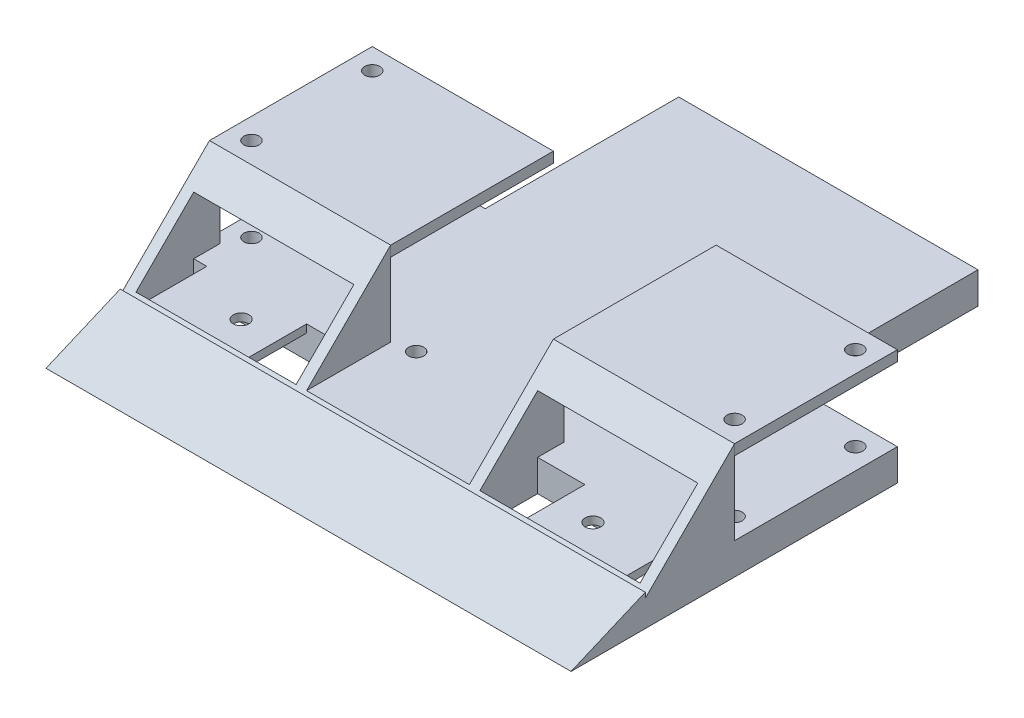
SolidWorks part; units mm, degrees
ref_plane "Front Plane" through (0, 0, 0) normal (0, 0, 1) x (1, 0, 0)
ref_plane "Top Plane" through (0, 0, 0) normal (0, 1, 0) x (1, 0, 0)
ref_plane "Right Plane" through (0, 0, 0) normal (1, 0, 0) x (0, 0, -1)
sketch "Sketch1" plane through (0, 0, 0) normal (0, 1, 0) x (1, 0, 0)
  line L1 (-50, 50) -> (50, 50)
  line L2 (-50, 50) -> (-50, -50)
  line L3 (-50, -50) -> (50, -50)
  line L4 (50, 50) -> (50, -50)
  line L5 (-50, 50) -> (50, -50) construction
  line L6 (-50, -50) -> (50, 50) construction
  point P0 (0, 0)
  dimension "D1" = 100
  dimension "D2" = 100
extrude "Boss-Extrude1" add sketch "Sketch1" along normal blind 6
sketch "Sketch2" plane through (50, 0, 0) normal (1, 0, 0) x (0, 0, -1)
  line L0 (-50, 0) -> (-35.8649, 6)
  line L1 (-50, 6) -> (50, 6) construction
  line L2 (-50, 0) -> (50, 0) construction
  line L3 (-35.8649, 6) -> (-50, 6)
  line L4 (-50, 6) -> (-50, 0)
  dimension "D1" = 23
extrude "Cut-Extrude1" cut sketch "Sketch2" against normal through all contours L0 L3 L4
sketch "Sketch3" plane through (50, 0, 0) normal (1, 0, 0) x (0, 0, -1)
  line L0 (-35.8649, 6) -> (-35.8649, 5)
  line L1 (-35.8649, 5) -> (-34.8649, 6)
  line L2 (-35.8649, 6) -> (50, 6) construction
  line L3 (-34.8649, 6) -> (-35.8649, 6)
  dimension "D1" = 1
extrude "Cut-Extrude3" cut sketch "Sketch3" against normal through all
sketch "Sketch4" plane through (0, 6, 0) normal (0, 1, 0) x (1, 0, 0)
  line L0 (50, -34.8649) -> (50, 50) construction
  line L1 (-50, 50) -> (50, 50)
  line L2 (-50, 50) -> (-50, 49)
  line L3 (-50, 49) -> (50, 49)
  line L4 (50, 50) -> (50, 49)
  dimension "D1" = 1
extrude "Cut-Extrude4" cut sketch "Sketch4" against normal through all
sketch "Sketch6" plane through (50, 0, 0) normal (1, 0, 0) x (0, 0, -1)
  line L0 (-34.8649, 6) -> (-18.8649, 22)
  line L1 (-18.8649, 22) -> (-18.8649, 6)
  line L2 (-34.8649, 6) -> (49, 6) construction
  line L3 (-18.8649, 6) -> (-34.8649, 6)
  dimension "D1" = 45
  dimension "D2" = 16
extrude "Boss-Extrude2" add sketch "Sketch6" against normal through all
sketch "Sketch8" plane through (0, 0, 18.8649) normal (0, 0, -1) x (-1, 0, 0)
  line L0 (50, 6) -> (50, 22) construction
  line L9 (-50, 22) -> (-15.5, 22)
  line L10 (-50, 22) -> (-50, 20)
  line L11 (-50, 20) -> (-15.5, 20)
  line L12 (-15.5, 22) -> (-15.5, 20)
  line L13 (15.5, 22) -> (50, 22)
  line L14 (15.5, 22) -> (15.5, 20)
  line L15 (15.5, 20) -> (50, 20)
  line L16 (50, 22) -> (50, 20)
  dimension "D1" = 2
  dimension "D5" = 2
extrude "Boss-Extrude3" add sketch "Sketch8" along normal blind 31 separate body
sketch "Sketch15" plane through (0, 6, 0) normal (0, 1, 0) x (1, 0, 0)
  line L1 (-50, 49) -> (-28.5, 49)
  line L2 (-50, 49) -> (-50, 12.14)
  line L3 (-50, 12.14) -> (-28.5, 12.14)
  line L4 (-28.5, 49) -> (-28.5, 12.14)
  line L5 (50, 49) -> (28.5, 49)
  line L6 (50, 49) -> (50, 12.14)
  line L7 (50, 12.14) -> (28.5, 12.14)
  line L8 (28.5, 49) -> (28.5, 12.14)
  dimension "D1" = 36.86
  dimension "D2" = 21.5
  dimension "D3" = 36.86
  dimension "D4" = 21.5
extrude "Cut-Extrude7" cut sketch "Sketch15" against normal through all
sketch "Sketch18" plane through (0, 0, 18.8649) normal (0, 0, -1) x (-1, 0, 0)
  line L0 (28.5, 6) -> (-28.5, 6) construction
  line L5 (15.5, 22) -> (-15.5, 22)
  line L6 (15.5, 22) -> (15.5, 6)
  line L7 (15.5, 6) -> (-15.5, 6)
  line L8 (-15.5, 22) -> (-15.5, 6)
extrude "Cut-Extrude8" cut sketch "Sketch18" against normal blind 48
sketch "Sketch19" plane through (0, 22, 0) normal (0, 1, 0) x (1, 0, 0)
  line L0 (-50, -18.8649) -> (-15.5, -18.8649) construction
  line L1 (-50, 12.1351) -> (-50, -18.8649) construction
  line L2 (50, 12.1351) -> (50, -18.8649) construction
  circle A0 centre (-46, -14.8649) radius 1.45
  circle A1 centre (-46, 8.1351) radius 1.45
  circle A2 centre (46, 8.1351) radius 1.45
  circle A3 centre (46, -14.8649) radius 1.45
  dimension "D1" = 2.9
  dimension "D4" = 23
  dimension "2.9" = 2.9
  dimension "D5" = 2.9
  dimension "D6" = 2.9
  dimension "D2" = 4
  dimension "D3" = 4
  dimension "D7" = 4
extrude "Cut-Extrude9" cut sketch "Sketch19" against normal through all
sketch "Sketch20" plane through (0, 6, 0) normal (0, 1, 0) x (1, 0, 0)
  line L0 (15.5, -34.8649) -> (-15.5, -34.8649) construction
  line L1 (-15.5, 12.1351) -> (-15.5, -18.8649) construction
  circle A0 centre (-11.5, -17.9949) radius 1.45
  circle A1 centre (11.5, -17.9949) radius 1.45
  dimension "D1" = 2.9
  dimension "D2" = 16.87
  dimension "2.9" = 2.9
  dimension "D3" = 4
  dimension "D4" = 23
extrude "Cut-Extrude10" cut sketch "Sketch20" against normal through all
sketch "Sketch23" plane through (0, 0, 18.8649) normal (0, 0, -1) x (-1, 0, 0)
  line L0 (28.5, 6) -> (-28.5, 6) construction
  line L1 (-48, 17) -> (-17.5, 17)
  line L2 (-48, 17) -> (-48, 6)
  line L3 (-48, 6) -> (-17.5, 6)
  line L4 (-17.5, 17) -> (-17.5, 6)
  line L5 (-50, 6) -> (-50, 22) construction
  line L6 (-15.5, 22) -> (-15.5, 6) construction
  line L7 (-50, 20) -> (-15.5, 20) construction
  line L8 (50, 6) -> (28.5, 6) construction
  line L9 (15.5, 6) -> (15.5, 22) construction
  line L10 (17.5, 17) -> (48, 17)
  line L11 (17.5, 17) -> (17.5, 6)
  line L12 (17.5, 6) -> (48, 6)
  line L13 (48, 17) -> (48, 6)
  line L14 (50, 6) -> (50, 22) construction
  line L15 (15.5, 20) -> (50, 20) construction
  dimension "D1" = 2
  dimension "D2" = 3
  dimension "2" = 2
  dimension "D3" = 2
  dimension "D4" = 2
  dimension "3" = 3
extrude "Cut-Extrude11" cut sketch "Sketch23" against normal through all
sketch "Sketch27" plane through (0, 0, 0) normal (0, -1, 0) x (1, 0, 0)
  line L11 (-48, 34.8649) -> (-17.5, 34.8649)
  line L12 (-48, 34.8649) -> (-48, 23.8649)
  line L13 (-48, 23.8649) -> (-17.5, 23.8649)
  line L14 (-17.5, 34.8649) -> (-17.5, 23.8649)
  line L15 (17.5, 34.8649) -> (48, 34.8649)
  line L16 (17.5, 34.8649) -> (17.5, 23.8649)
  line L17 (17.5, 23.8649) -> (48, 23.8649)
  line L18 (48, 34.8649) -> (48, 23.8649)
extrude "Cut-Extrude14" cut sketch "Sketch27" against normal blind 10
ref_plane "Plane1" through (-50, 6, 35.8649) normal (1, 0, 0) x (0, 0, -1)
sketch "Sketch32" plane through (0, 0, 23.8649) normal (0, 0, 1) x (1, 0, 0)
  line L0 (-17.5, 6) -> (-48, 6) construction
  line L1 (-45.5, 6) -> (-26.5, 6)
  line L2 (-45.5, 6) -> (-45.5, 4.5)
  line L3 (-45.5, 4.5) -> (-26.5, 4.5)
  line L4 (-26.5, 6) -> (-26.5, 4.5)
  line L5 (-48, 6) -> (-48, 0) construction
  line L6 (48, 6) -> (17.5, 6) construction
  line L7 (45.5, 6) -> (26.5, 6)
  line L8 (45.5, 6) -> (45.5, 4.5)
  line L9 (45.5, 4.5) -> (26.5, 4.5)
  line L10 (26.5, 6) -> (26.5, 4.5)
  line L11 (48, 6) -> (48, 0) construction
  dimension "D1" = 1.5
  dimension "D2" = 2.5
  dimension "D3" = 1.5
  dimension "D4" = 19
  dimension "D5" = 19
  dimension "D6" = 2.5
extrude "Boss-Extrude6" add sketch "Sketch32" along normal up to surface (11 mm away) up to face at (-32.75, 3, 34.8649)
sketch "Sketch33" plane through (0, 0, 0) normal (0, -1, 0) x (1, 0, 0)
  circle A0 centre (-33.5, 29.3405) radius 1.5
  circle A1 centre (33.5, 29.3405) radius 1.5
extrude "Cut-Extrude15" cut sketch "Sketch33" against normal blind 6
